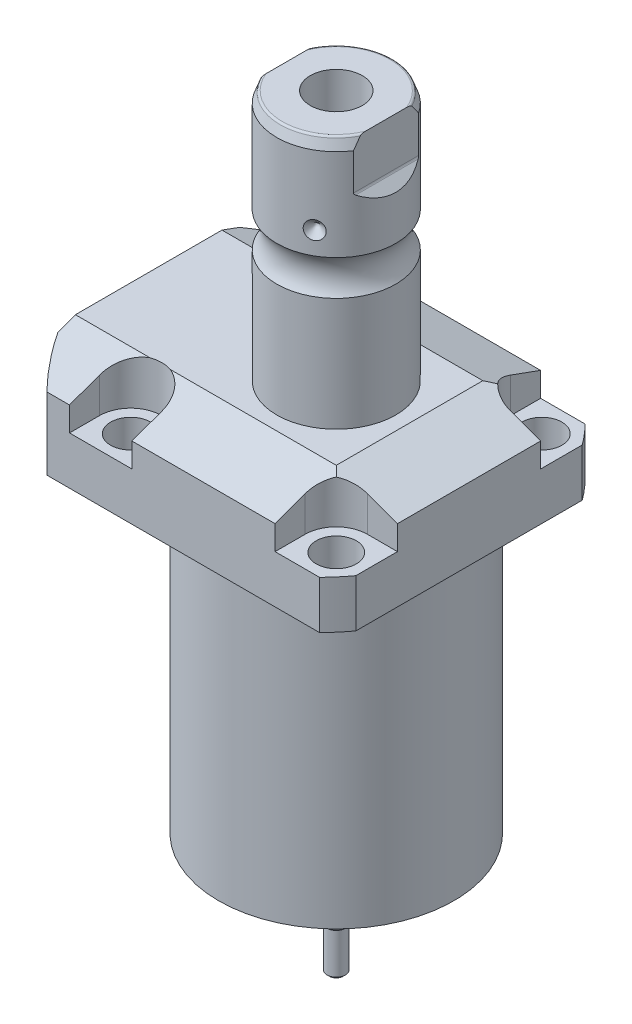
SolidWorks part; units mm, degrees
material "Alloy Steel"
ref_plane "Front Plane" through (0, 0, 0) normal (0, 0, 1) x (1, 0, 0)
ref_plane "Top Plane" through (0, 0, 0) normal (0, 1, 0) x (1, 0, 0)
ref_plane "Right Plane" through (0, 0, 0) normal (1, 0, 0) x (0, 0, -1)
sketch "Sketch1" plane through (0, 0, 0) normal (0, -1, 0) x (0, 0, 1)
  line L0 (-35.433, 50.063) -> (35.433, 50.063)
  line L1 (35.433, 50.063) -> (35.433, -35.433)
  line L2 (35.433, -35.433) -> (-35.433, -35.433)
  line L3 (-35.433, -35.433) -> (-35.433, 50.063)
  line L4 (0, 0) -> (0, -60.6467) construction
  dimension "D1" = 35.433
  dimension "D2" = 85.496
  dimension "D3" = 70.866
extrude "Extrude1" add sketch "Sketch1" against normal blind 104.521
sketch "Sketch2" plane through (0, 0, 0) normal (0, -1, 0) x (1, 0, 0)
  circle A0 centre (-5.4102, 0) radius 50.8
  dimension "D1" = 101.6
  dimension "D2" = 5.4102
extrude "Cut-Extrude1" cut sketch "Sketch2" against normal through all flip side to cut
sketch "Sketch3" plane through (0, 0, 0) normal (1, 0, 0) x (0, 0, -1)
  line L0 (31.3945, 0) -> (31.3945, 79.502)
  line L1 (31.3945, 79.502) -> (76.5937, 79.502)
  line L2 (76.5937, 79.502) -> (76.5937, 0)
  line L3 (76.5937, 0) -> (31.3945, 0)
  line L4 (0, -93.345) -> (0, 4.445) construction
  line L5 (24.2233, 0) -> (-24.2233, 0) construction
  dimension "D1" = 62.789
  dimension "D2" = 153.1874
  dimension "D3" = 79.502
revolve "Cut-Revolve1" cut sketch "Sketch3" angle 360 about L4
fillet "Fillet1" radius 0.381 1 edges at (0, 79.502, -31.3945)
sketch "Sketch4" plane through (0, 104.521, 0) normal (0, 1, 0) x (-1, 0, 0)
  line L0 (-35.433, -30.2072) -> (-35.433, 30.2072) construction
  line L1 (41.8127, 35.433) -> (-30.9923, 35.433) construction
  line L2 (-19.1008, -35.433) -> (-19.1008, -27.432)
  line L3 (-35.433, -35.433) -> (-19.1008, -35.433)
  line L4 (-35.433, -19.1008) -> (-35.433, -35.433)
  line L5 (-27.432, -19.1008) -> (-35.433, -19.1008)
  line L6 (35.7632, -35.433) -> (19.1008, -35.433)
  line L7 (19.1008, 35.433) -> (19.1008, 27.432)
  line L8 (35.7632, 35.433) -> (35.7632, 27.432)
  line L9 (35.7632, 35.433) -> (19.1008, 35.433)
  line L10 (-27.432, 19.1008) -> (-35.433, 19.1008)
  line L11 (-35.433, 19.1008) -> (-35.433, 35.433)
  line L12 (-35.433, 35.433) -> (-19.1008, 35.433)
  line L13 (-19.1008, 35.433) -> (-19.1008, 27.432)
  line L14 (-48.9217, 0) -> (49.4551, 0) construction
  line L15 (35.7632, -35.433) -> (35.7632, -27.432)
  line L16 (19.1008, -35.433) -> (19.1008, -27.432)
  arc A0 (19.1008, -27.432) -> (35.7632, -27.432) centre (27.432, -27.432) cw
  arc A1 (-27.432, -19.1008) -> (-19.1008, -27.432) centre (-27.432, -27.432) cw
  arc A2 (-27.432, 19.1008) -> (-19.1008, 27.432) centre (-27.432, 27.432) ccw
  arc A3 (19.1008, 27.432) -> (35.7632, 27.432) centre (27.432, 27.432) ccw
  dimension "D2" = 8.3312
  dimension "D1" = 27.432
  dimension "D3" = 27.432
  dimension "D4" = 54.864
extrude "Cut-Extrude2" cut sketch "Sketch4" against normal blind 12.243
sketch "Sketch5" plane through (0, 0, 0) normal (1, 0, 0) x (0, 0, -1)
  line L0 (-19.558, 104.521) -> (-35.433, 98.743)
  line L1 (0, 0) -> (0, 154.1081) construction
  line L2 (-19.558, 104.521) -> (-35.433, 104.521)
  line L3 (-35.433, 104.521) -> (-35.433, 98.743)
  dimension "D1" = 15.875
  dimension "D2" = 20
extrude "Cut-Extrude9" cut sketch "Sketch5" against normal through all and the other way through all
mirror "Mirror1" about plane through (0, 0, 0) normal (0, 0, 1) of "Cut-Extrude9"
sketch "Sketch9" plane through (0, 0, 0) normal (0, 0, 1) x (1, 0, 0)
  line L0 (19.558, 104.521) -> (35.433, 98.743)
  line L1 (35.433, 98.743) -> (35.433, 104.521)
  line L2 (35.433, 104.521) -> (19.558, 104.521)
  dimension "D1" = 15.875
  dimension "D2" = 20
extrude "Cut-Extrude7" cut sketch "Sketch9" against normal through all and the other way through all
ref_plane "Plane14" through (-35.0774, 0, 0) normal (1, 0, 0) x (0, 0, -1)
sketch "Sketch20" plane through (-35.0774, 88.9, -18.1102) normal (1, 0, 0) x (0, 1, 0)
  line L0 (-88.9, 18.1102) -> (39.8401, 18.1102) construction
  line L1 (-7.2797, 32.639) -> (36.9042, 32.639) construction
  line L2 (-9.398, 38.3413) -> (-7.9502, 38.3413)
  line L3 (-9.398, -6.1131) -> (-9.398, 42.3335) construction
  line L4 (-7.9502, 38.3413) -> (-7.9502, 35.8902)
  line L5 (-7.9502, 35.8902) -> (-6.9342, 35.8902)
  line L6 (-6.9342, 35.8902) -> (-6.9342, 33.8836)
  line L7 (-6.9342, 33.8836) -> (4.0386, 33.8836)
  line L8 (4.0386, 33.8836) -> (4.0386, 32.639)
  line L9 (4.0386, 32.639) -> (-9.398, 32.639)
  line L10 (-9.398, 38.3413) -> (-9.398, 32.639)
  dimension "D1" = 14.5288
  dimension "D2" = 11.4046
  dimension "D3" = 1.4478
  dimension "D4" = 6.5024
  dimension "D5" = 1.016
  dimension "D6" = 2.4892
  dimension "D7" = 10.9728
revolve "Cut-Revolve4" cut sketch "Sketch20" angle 360 about L1
mirror "Mirror10" about plane through (0, 0, 0) normal (0, 0, 1) of "Cut-Revolve4"
sketch "Sketch10" plane through (-35.0774, 88.9, -18.1102) normal (1, 0, 0) x (0, 1, 0)
  line L0 (-1.0325, 3.5814) -> (1.5659, 3.5814) construction
  line L1 (4.0386, 4.826) -> (-6.9342, 4.826) construction
  line L2 (-6.9342, 2.3368) -> (4.0386, 2.3368) construction
  line L4 (-9.398, -12.097) -> (-9.398, 48.3174) construction
  circle A0 centre (-9.1313, 8.1026) radius 1.1811
  dimension "D1" = 2.3622
  dimension "D2" = 0.2667
  dimension "D3" = 9.0424
revolve "Revolve4" add sketch "Sketch10" angle 360 about L0
mirror "Mirror12" about plane through (0, 0, 0) normal (0, 0, 1) of bodies 135
sketch "Sketch15" plane through (0, 0, 0) normal (1, 0, 0) x (0, 0, -1)
  line L0 (0, 104.521) -> (15.875, 104.521)
  line L1 (15.875, 104.521) -> (15.875, 134.7639)
  line L2 (15.875, 144.1781) -> (15.875, 168.656)
  line L3 (14.8118, 171.577) -> (0, 171.577)
  line L4 (0, 171.577) -> (0, 104.521)
  line L5 (0, 250.2908) -> (0, 28.9095) construction
  line L6 (19.558, 104.521) -> (-19.558, 104.521) construction
  line L7 (14.8118, 171.577) -> (15.875, 168.656)
  line L8 (-31.3945, 0) -> (31.3945, 0) construction
  arc A0 (15.875, 144.1781) -> (15.875, 134.7639) centre (22.2504, 139.471) ccw
  dimension "D2" = 20
  dimension "D4" = 7.9248
  dimension "D6" = 28.6512
  dimension "D1" = 171.577
  dimension "D3" = 31.75
  dimension "D5" = 32.106
  dimension "D7" = 2.921
revolve "Revolve3" add sketch "Sketch15" angle 360 about L5
hole_wizard "Hole1" positions "Sketch18" profile "Sketch17" legacy end condition up to next
sketch "Sketch18" plane through (0, 92.278, 0) normal (0, 1, 0) x (-1, 0, 0)
  arc A0 (35.7632, -27.432) -> (19.1008, -27.432) centre (27.432, -27.432) ccw construction
  arc A1 (19.1008, 27.432) -> (35.7632, 27.432) centre (27.432, 27.432) ccw construction
  arc A2 (-27.432, 19.1008) -> (-19.1008, 27.432) centre (-27.432, 27.432) ccw construction
  arc A3 (-19.1008, -27.432) -> (-27.432, -19.1008) centre (-27.432, -27.432) ccw construction
  point P0 (-27.432, -27.432)
  point P1 (-27.432, 27.432)
  point P3 (27.432, 27.432)
  point P5 (27.432, -27.432)
sketch "Sketch17" plane through (27.432, 92.278, -27.432) normal (1, 0, 0) x (0, 0, 1)
  line L0 (0, 0) -> (0, 12.776)
  line L1 (0, 12.776) -> (5.3594, 12.776)
  line L2 (5.3594, 12.776) -> (5.3594, 0)
  line L3 (5.3594, 0) -> (0, 0)
  line L4 (0, 110) -> (0, -10) construction
  dimension "Diameter" = 10.7188
  dimension "Depth" = 12.776
chamfer "Chamfer1" distance 0.635 angle 45 2 edges at (-35.0774, 81.9658, 13.2842) (-35.0774, 81.9658, -13.2842)
ref_plane "Plane15" through (0, 92.5068, 0) normal (0, -1, 0) x (1, 0, 0)
sketch "Sketch21" plane through (0, 92.5068, 0) normal (0, -1, 0) x (1, 0, 0)
  line L0 (-57.5495, -12.9794) -> (-2.9353, -12.9794) construction
  line L1 (-50.063, -1.9304) -> (-49.809, -1.9304)
  line L2 (-49.809, -1.9304) -> (-49.809, -6.3246)
  line L3 (-49.809, -6.3246) -> (-49.0978, -7.0358)
  line L4 (-49.0978, -7.0358) -> (-35.6358, -7.0358)
  line L5 (-35.6358, -7.0358) -> (-35.6358, -12.9794)
  line L6 (-35.6358, -12.9794) -> (-50.063, -12.9794)
  line L7 (-50.063, 24.2233) -> (-50.063, -24.2233) construction
  line L8 (-50.063, -12.9794) -> (-50.063, -1.9304)
  dimension "D1" = 12.9794
  dimension "D2" = 0.254
  dimension "D3" = 22.098
  dimension "D4" = 45
  dimension "D5" = 0.7112
  dimension "D6" = 11.8872
  dimension "D7" = 14.1732
revolve "Cut-Revolve5" cut sketch "Sketch21" angle 360 about L0
mirror "Mirror13" about plane through (0, 0, 0) normal (0, 0, 1) of "Cut-Revolve5"
fillet "Fillet2" radius 0.635 1 edges at (0, 171.577, 14.8118)
sketch "Sketch26" plane through (0, 0, 0) normal (0, 0, 1) x (1, 0, 0)
  line L0 (-39.772, 150.159) -> (35.3173, 150.159) construction
  line L1 (-15.875, 152.572) -> (-13.462, 150.159)
  line L2 (-15.875, 168.656) -> (-15.875, 144.1781) construction
  line L3 (-13.462, 150.159) -> (-15.875, 150.159)
  line L4 (-15.875, 150.159) -> (-15.875, 152.572)
  arc A0 (-15.875, 134.7639) -> (-15.875, 144.1781) centre (-22.2504, 139.471) ccw construction
  dimension "D1" = 45
  dimension "D2" = 4.826
  dimension "D3" = 10.688
revolve "Cut-Revolve7" cut sketch "Sketch26" angle 360 about L0
pattern_circular "CirPattern1" count 3 over 360 about axis through (0, 250.2908, 0) along (0, 1, 0) of "Cut-Revolve7"
hole_wizard "Hole2" positions "Sketch28" profile "Sketch27" legacy
sketch "Sketch28" plane through (0, 171.577, 0) normal (0, 1, 0) x (-1, 0, 0)
  circle A0 centre (0, 0) radius 15.875 construction
  point P0 (0, 0)
sketch "Sketch27" plane through (0, 171.577, 0) normal (1, 0, 0) x (0, 0, 1)
  line L0 (0, 0) -> (0, 29.5665)
  line L1 (0, 29.5665) -> (6.9342, 25.4)
  line L2 (6.9342, 25.4) -> (6.9342, 0)
  line L4 (6.9342, 0) -> (0, 0)
  line L6 (0, 29.5665) -> (-6.9342, 25.4) construction
  line L7 (0, -4.2442) -> (0, 117.3081) construction
  dimension "Diameter" = 13.8684
  dimension "Depth" = 25.4
  dimension "Drill Angle" = 118
sketch "Sketch29" plane through (0, 0, 0) normal (0, 0, 1) x (1, 0, 0)
  line L0 (0, 0) -> (0, 192.0172) construction
  line L1 (13.284, 171.577) -> (13.284, 158.877)
  line L2 (14.3672, 171.577) -> (-14.3672, 171.577) construction
  line L3 (13.5072, 158.3382) -> (15.875, 155.9704)
  line L5 (15.875, 155.9704) -> (15.875, 171.577)
  line L6 (15.875, 171.577) -> (13.284, 171.577)
  line L7 (-15.875, 171.577) -> (-13.284, 171.577)
  line L8 (-15.875, 155.9704) -> (-15.875, 171.577)
  line L9 (-13.5072, 158.3382) -> (-15.875, 155.9704)
  line L10 (-13.284, 171.577) -> (-13.284, 158.877)
  arc A0 (13.284, 158.877) -> (13.5072, 158.3382) centre (14.046, 158.877) ccw
  arc A1 (-13.284, 158.877) -> (-13.5072, 158.3382) centre (-14.046, 158.877) cw
  dimension "D2" = 0.762
  dimension "D1" = 45
  dimension "D3" = 26.568
  dimension "D4" = 12.7
extrude "Cut-Extrude10" cut sketch "Sketch29" against normal through all and the other way through all
sketch "Sketch30" plane through (0, 0, 0) normal (1, 0, 0) x (0, 0, -1)
  line L0 (0, -1000) -> (0, 49000) construction
  line L1 (0, 0) -> (3.175, 0)
  line L2 (-31.3945, 0) -> (31.3945, 0) construction
  line L3 (3.175, 0) -> (3.175, -19.5526)
  line L4 (3.175, -19.5526) -> (2.4384, -20.8284)
  line L5 (2.4384, -20.8284) -> (2.4384, -31.6234)
  line L6 (2.4384, -31.6234) -> (1.8034, -32.2584)
  line L7 (1.8034, -32.2584) -> (0, -32.2584)
  line L8 (0, -32.2584) -> (0, 0)
  line L9 (-5.4728, 171.577) -> (-14.3672, 171.577) construction
  dimension "D1" = 45
  dimension "D2" = 0.635
  dimension "D3" = 4.8768
  dimension "D4" = 30
  dimension "D5" = 6.35
  dimension "D6" = 11.43
  dimension "D7" = 203.8354
revolve "Revolve5" add sketch "Sketch30" angle 360 about L0
sketch "Sketch33" plane through (0, 0, 0) normal (1, 0, 0) x (0, 0, -1)
  line L0 (0, -1000) -> (0, 49000) construction
  line L1 (2.5019, -32.2584) -> (2.5019, -16.3834)
  line L2 (-1.8034, -32.2584) -> (1.8034, -32.2584) construction
  line L3 (2.5019, -16.3834) -> (3.175, -15.7103)
  line L4 (3.175, -19.5526) -> (3.175, 0) construction
  line L5 (3.175, -15.7103) -> (3.175, -32.2584)
  line L6 (3.175, -32.2584) -> (2.5019, -32.2584)
  line L7 (-3.175, -32.2584) -> (-2.5019, -32.2584)
  line L8 (-2.5019, -32.2584) -> (-2.5019, -16.3834)
  line L9 (-3.175, -15.7103) -> (-3.175, -32.2584)
  line L10 (-2.5019, -16.3834) -> (-3.175, -15.7103)
  dimension "D1" = 5.0038
  dimension "D2" = 15.875
  dimension "D3" = 45
extrude "Cut-Extrude11" cut sketch "Sketch33" against normal mid plane 7.62
sketch "Sketch34" plane through (0, 0, 0) normal (1, 0, 0) x (0, 0, -1)
  line L0 (0, -1000) -> (0, 49000) construction
  line L1 (-31.3945, 0) -> (31.3945, 0) construction
  line L2 (11.6459, 0) -> (14.351, 0)
  line L3 (11.6459, 0) -> (11.6459, 1.3208)
  line L4 (11.6459, 1.3208) -> (14.351, 1.3208)
  line L5 (14.351, 0) -> (14.351, 1.3208)
  dimension "D1" = 23.2918
  dimension "D2" = 28.7021
  dimension "D3" = 1.3208
revolve "Cut-Revolve8" cut sketch "Sketch34" angle 360 about L0
sketch "Sketch35" plane through (0, 0, 0) normal (0, -1, 0) x (1, 0, 0)
  line L0 (-1000, 0) -> (49000, 0) construction
  line L1 (0, 0) -> (48296.2913, -12940.9523) construction
  line L2 (0, 0) -> (25000, 43301.2702) construction
  circle A0 centre (0, 0) radius 19.431 construction
  circle A1 centre (19.431, 0) radius 1.27
  circle A2 centre (18.7689, -5.0291) radius 1.27
  circle A3 centre (-13.7398, 13.7398) radius 1.27
  circle A4 centre (-9.7155, 16.8278) radius 1.27
  circle A5 centre (-13.7398, -13.7398) radius 1.27
  circle A6 centre (-9.7155, -16.8278) radius 1.27
  dimension "D3" = 38.8621
  dimension "D4" = 2.54
  dimension "D5" = 2.54
  dimension "D1" = 15
  dimension "D2" = 60
extrude "Cut-Extrude12" cut sketch "Sketch35" against normal blind 7.62
